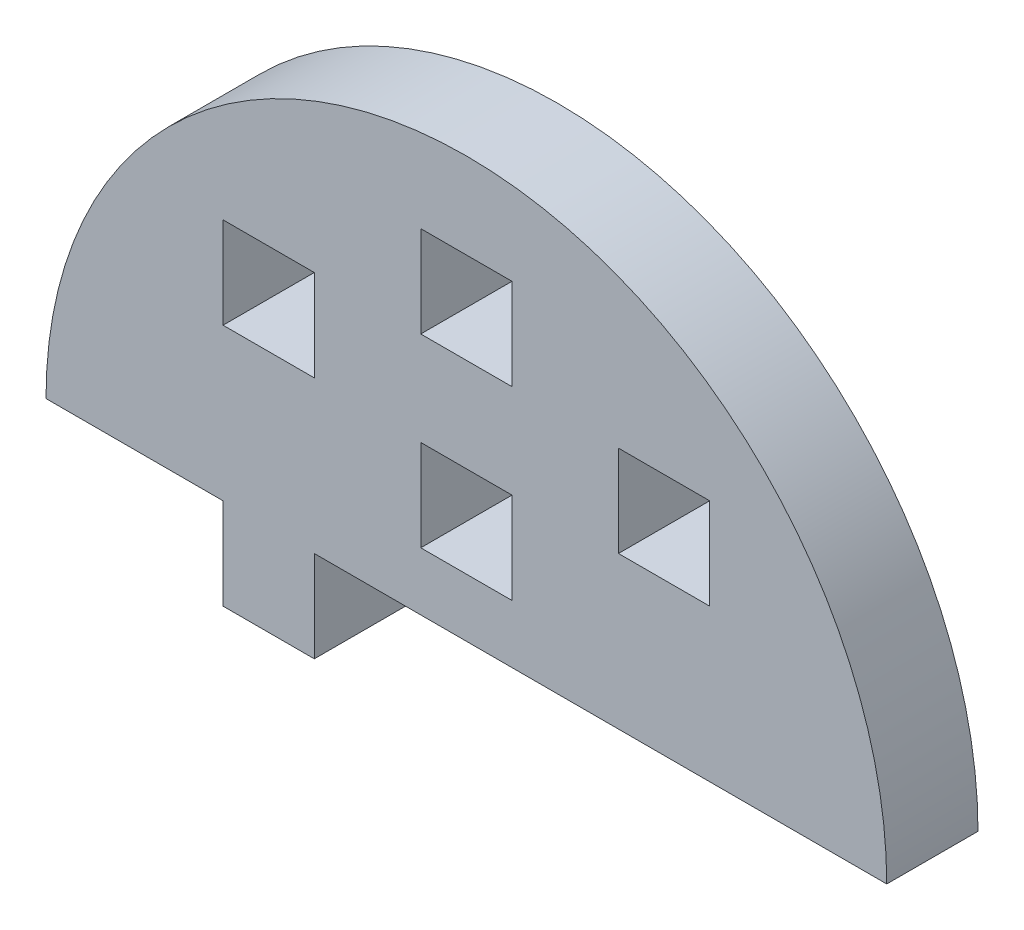
SolidWorks part; units mm, degrees
ref_plane "Front Plane" through (0, 0, 0) normal (0, 0, 1) x (1, 0, 0)
ref_plane "Top Plane" through (0, 0, 0) normal (0, 1, 0) x (1, 0, 0)
ref_plane "Right Plane" through (0, 0, 0) normal (1, 0, 0) x (0, 0, -1)
sketch "Model" plane through (0, 0, 0) normal (0, 0, 1) x (1, 0, 0)
  line L0 (3491.8473, 1193.0171) -> (3491.8473, 1187.0171)
  line L1 (3491.8473, 1187.0171) -> (3485.8473, 1187.0171)
  line L2 (3485.8473, 1187.0171) -> (3485.8473, 1193.0171)
  line L3 (3511.8473, 1209.0171) -> (3517.8473, 1209.0171)
  line L4 (3517.8473, 1209.0171) -> (3517.8473, 1203.0171)
  line L5 (3517.8473, 1203.0171) -> (3511.8473, 1203.0171)
  line L6 (3511.8473, 1203.0171) -> (3511.8473, 1209.0171)
  line L7 (3491.8473, 1209.0171) -> (3485.8473, 1209.0171)
  line L8 (3485.8473, 1209.0171) -> (3485.8473, 1203.0171)
  line L9 (3485.8473, 1203.0171) -> (3491.8473, 1203.0171)
  line L10 (3491.8473, 1203.0171) -> (3491.8473, 1209.0171)
  line L11 (3498.8473, 1215.0171) -> (3504.8473, 1215.0171)
  line L12 (3504.8473, 1215.0171) -> (3504.8473, 1209.0171)
  line L13 (3504.8473, 1209.0171) -> (3498.8473, 1209.0171)
  line L14 (3498.8473, 1209.0171) -> (3498.8473, 1215.0171)
  line L15 (3498.8473, 1196.8416) -> (3504.8473, 1196.8416)
  line L16 (3504.8473, 1196.8416) -> (3504.8473, 1202.8416)
  line L17 (3504.8473, 1202.8416) -> (3498.8473, 1202.8416)
  line L18 (3498.8473, 1202.8416) -> (3498.8473, 1196.8416)
  line L19 (3474.2044, 1193.0171) -> (3485.8473, 1193.0171)
  line L20 (3491.8473, 1193.0171) -> (3529.4901, 1193.0171)
  arc A0 (3529.4901, 1193.0171) -> (3474.2044, 1193.0171) centre (3501.8473, 1193.0171) ccw
extrude "Boss-Extrude1" add sketch "Model" along normal blind 6 contours L9 L10 L7 L8 | L14 L13 L12 L11 | L17 L18 L15 L16 | L6 L5 L4 L3 | A0 L19 L2 L1 L0 L20
